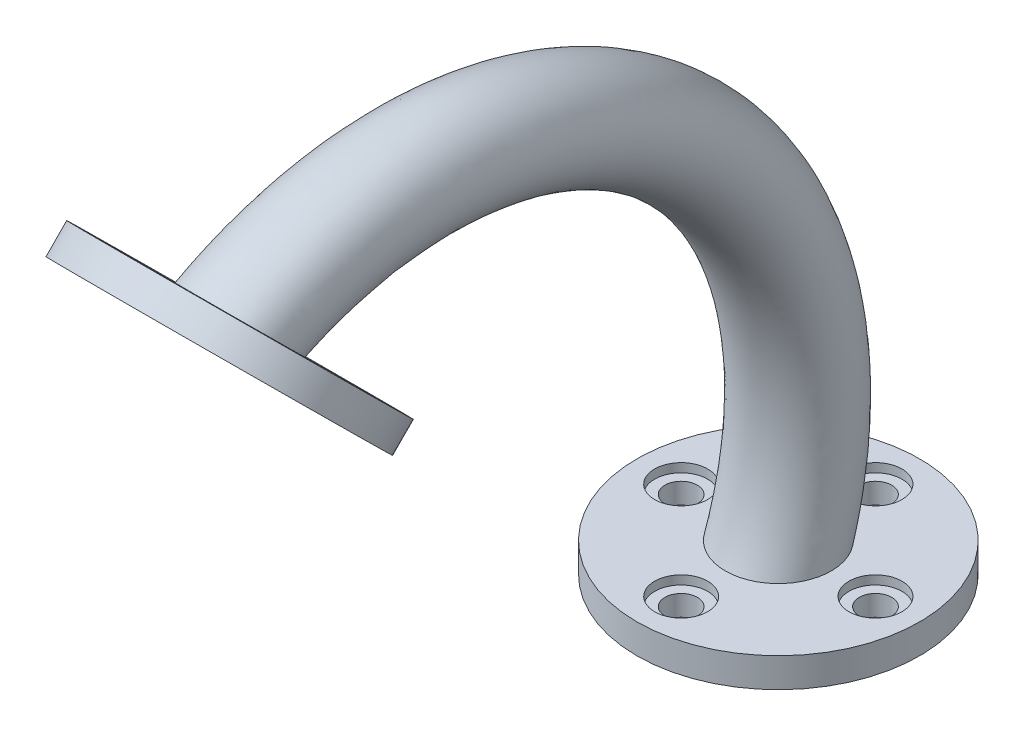
SolidWorks part; units mm, degrees
ref_plane "Alzado" through (0, 0, 0) normal (0, 0, 1) x (1, 0, 0)
ref_plane "Planta" through (0, 0, 0) normal (0, 1, 0) x (1, 0, 0)
ref_plane "Vista lateral" through (0, 0, 0) normal (1, 0, 0) x (0, 0, -1)
sketch "Croquis1" plane through (0, 0, 0) normal (0, 1, 0) x (1, 0, 0)
  line L0 (-48, 0) -> (48, 0) construction
  line L1 (0, 48) -> (0, -48) construction
  line L2 (0, 0) -> (0, 33) construction
  line L3 (0, 0) -> (33, 0) construction
  circle A0 centre (0, 0) radius 48
  circle A1 centre (0, 0) radius 13.5
  circle A2 centre (0, 33) radius 5.5 construction
  circle A3 centre (33, 0) radius 5.5 construction
  circle A4 centre (0, -33) radius 5.5 construction
  circle A5 centre (-33, 0) radius 5.5 construction
  point P7 (0, 0)
  point P10 (0, 0)
  dimension "D1" = 96
  dimension "D2" = 27
  dimension "D3" = 11
  dimension "D4" = 33
  dimension "D6" = 90
  dimension "D7" = 33
  dimension "D5" = 4
extrude "Saliente-Extruir3" add sketch "Croquis1" along normal blind 10
hole_wizard "Taladro1" positions "Croquis5" profile "Croquis7" legacy
sketch "Croquis5" plane through (0, 10, 0) normal (0, 1, 0) x (1, 0, 0)
  point P0 (-33, 0)
  point P3 (0, 33)
  point P6 (33, 0)
  point P9 (0, -33)
sketch "Croquis7" plane through (-33, 10, 0) normal (1, 0, 0) x (0, 0, 1)
  line L0 (0, 0) -> (0, 103.3047)
  line L1 (0, 103.3047) -> (5.5, 100)
  line L2 (5.5, 100) -> (5.5, 3)
  line L3 (5.5, 3) -> (9, 3)
  line L4 (9, 0) -> (0, 0)
  line L5 (0, -11.3109) -> (0, 121.1557) construction
  line L6 (0, 103.3047) -> (-5.5, 100) construction
  line L7 (9, 3) -> (9, 0)
  dimension "Diámetro" = 11
  dimension "Profundidad" = 100
  dimension "Diámetro de refrentado 1" = 18
  dimension "Profundidad de refrentado 1" = 3
  dimension "Ángulo de perforado" = 118
sketch "Croquis9" plane through (0, 10, 0) normal (0, 1, 0) x (1, 0, 0)
  circle A0 centre (0, 0) radius 13.5
  circle A1 centre (0, 0) radius 18
  dimension "D1" = 27
  dimension "D2" = 36
sketch "Croquis10" plane through (0, 0, 0) normal (0, 1, 0) x (1, 0, 0)
sketch "Croquis14" plane through (0, 0, 0) normal (1, 0, 0) x (0, 0, -1)
  line L0 (0, 0) -> (0, 10) construction
  line L1 (13.5, 10) -> (-13.5, 10) construction
  arc A0 (0, 10) -> (-182.806, 166.2207) centre (-123.522, 50.5254) ccw
  dimension "D1" = 130
sweep "Barrer2" add profiles "Croquis9" path "Croquis14"
sketch "Croquis15" plane through (0, -7.432, 7.3559) normal (0, -0.7107, 0.7035) x (1, 0, 0)
  line L0 (0, 246.8563) -> (0, 279.8563) construction
  line L1 (0, 249.8563) -> (0, 279.8563) construction
  circle A1 centre (0, 246.8563) radius 48
  circle A2 centre (0, 246.8563) radius 13.5
  circle A3 centre (0, 279.8563) radius 5.5 construction
  circle A4 centre (30, 249.8563) radius 5.5 construction
  circle A5 centre (0, 219.8563) radius 5.5 construction
  circle A6 centre (-30, 249.8563) radius 5.5 construction
  dimension "D1" = 96
  dimension "D3" = 11
  dimension "D2" = 33
  dimension "D5" = 30
  dimension "D4" = 4
extrude "Saliente-Extruir5" add sketch "Croquis15" along normal blind 10
hole_wizard "Taladro3" positions "Croquis20" profile "Croquis21" legacy
sketch "Croquis20" plane through (0, -7.432, 7.3559) normal (0, 0.7107, -0.7035) x (1, 0, 0)
  point P0 (30, -249.8563)
  point P3 (0, -279.8563)
  point P6 (-30, -249.8563)
  point P9 (0, -219.8563)
sketch "Croquis21" plane through (30, 168.3311, 184.9382) normal (1, 0, 0) x (0, 0.7035, 0.7107)
  line L0 (0, 0) -> (0, 103.3047)
  line L1 (0, 103.3047) -> (5.5, 100)
  line L2 (5.5, 100) -> (5.5, 3)
  line L3 (5.5, 3) -> (9, 3)
  line L4 (9, 0) -> (0, 0)
  line L5 (0, -11.3109) -> (0, 121.1557) construction
  line L6 (0, 103.3047) -> (-5.5, 100) construction
  line L7 (9, 3) -> (9, 0)
  dimension "Diámetro" = 11
  dimension "Profundidad" = 100
  dimension "Diámetro de refrentado 1" = 18
  dimension "Profundidad de refrentado 1" = 3
  dimension "Ángulo de perforado" = 118
